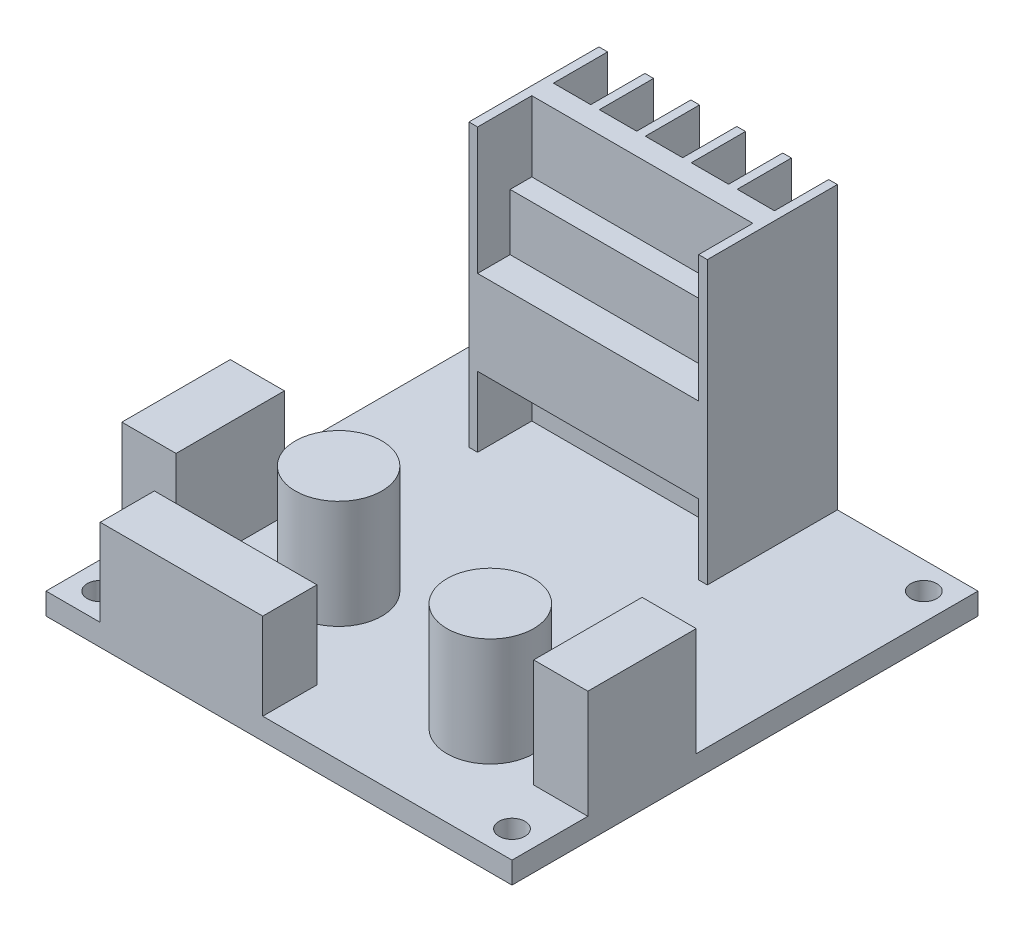
SolidWorks part; units mm, degrees
ref_plane "前视基准面" through (0, 0, 0) normal (0, 0, 1) x (1, 0, 0)
ref_plane "上视基准面" through (0, 0, 0) normal (0, 1, 0) x (1, 0, 0)
ref_plane "右视基准面" through (0, 0, 0) normal (1, 0, 0) x (0, 0, -1)
sketch "草图1" plane through (0, 0, 0) normal (0, 1, 0) x (1, 0, 0)
  line L1 (-21.5, 21.5) -> (21.5, 21.5)
  line L2 (-21.5, 21.5) -> (-21.5, -21.5)
  line L3 (-21.5, -21.5) -> (21.5, -21.5)
  line L4 (21.5, 21.5) -> (21.5, -21.5)
  dimension "D1" = 43
  dimension "D2" = 43
  dimension "D3" = 21.5
  dimension "D4" = 21.5
extrude "凸台-拉伸1" add sketch "草图1" along normal blind 2
sketch "草图2" plane through (0, 0, 0) normal (0, 1, 0) x (1, 0, 0)
  line L0 (-21.5, -21.5) -> (21.5, -21.5) construction
  line L1 (-16.5, -16.5) -> (-1.5, -16.5)
  line L2 (-16.5, -16.5) -> (-16.5, -21.5)
  line L3 (-16.5, -21.5) -> (-1.5, -21.5)
  line L4 (-1.5, -16.5) -> (-1.5, -21.5)
  line L5 (-21.5, 21.5) -> (-21.5, -21.5) construction
  dimension "D1" = 5
  dimension "D2" = 15
  dimension "D3" = 5
extrude "凸台-拉伸2" add sketch "草图2" along normal blind 10
sketch "草图3" plane through (0, 2, 0) normal (0, 1, 0) x (1, 0, 0)
  line L0 (-21.5, 21.5) -> (-21.5, -21.5) construction
  line L1 (-16.5, -4.5) -> (-21.5, -4.5)
  line L2 (-16.5, -4.5) -> (-16.5, -14.5)
  line L3 (-16.5, -14.5) -> (-21.5, -14.5)
  line L4 (-21.5, -4.5) -> (-21.5, -14.5)
  line L5 (-21.5, -21.5) -> (-16.5, -21.5) construction
  dimension "D1" = 7
  dimension "D2" = 5
  dimension "D3" = 10
extrude "凸台-拉伸3" add sketch "草图3" along normal blind 10
sketch "草图4" plane through (0, 2, 0) normal (0, 1, 0) x (1, 0, 0)
  line L0 (21.5, -21.5) -> (21.5, 21.5) construction
  line L1 (16.5, -4.5) -> (21.5, -4.5)
  line L2 (16.5, -4.5) -> (16.5, -14.5)
  line L3 (16.5, -14.5) -> (21.5, -14.5)
  line L4 (21.5, -4.5) -> (21.5, -14.5)
  line L5 (-1.5, -21.5) -> (21.5, -21.5) construction
  dimension "D1" = 7
  dimension "D2" = 10
  dimension "D3" = 5
extrude "凸台-拉伸4" add sketch "草图4" along normal blind 10
sketch "草图5" plane through (0, 2, 0) normal (0, 1, 0) x (1, 0, 0)
  circle A0 centre (-8, -8) radius 4
  point P2 (0, 0)
  point P3 (-6.2464, -8.5132)
  point P4 (0, 0)
  point P5 (0, 0)
extrude "凸台-拉伸5" add sketch "草图5" along normal blind 10
sketch "草图6" plane through (0, 2, 0) normal (0, 1, 0) x (1, 0, 0)
  circle A0 centre (10, -12) radius 4
extrude "凸台-拉伸6" add sketch "草图6" along normal blind 10
sketch "草图7" plane through (0, 2, 0) normal (0, 1, 0) x (1, 0, 0)
  line L0 (21.5, 21.5) -> (-21.5, 21.5) construction
  line L1 (0, 21.5) -> (-13.4757, 21.5)
  line L3 (8.5243, 9.5) -> (-13.4757, 9.5)
  line L4 (-13.4757, 21.5) -> (-13.4757, 9.5)
  line L5 (8.5243, 9.5) -> (8.5243, 21.5)
  line L6 (8.5243, 21.5) -> (-13.4757, 21.5)
extrude "凸台-拉伸7" add sketch "草图7" along normal blind 26 contours L4 L3 L5 L6
sketch "草图8" plane through (0, 0, -21.5) normal (0, 0, -1) x (-1, 0, 0)
  line L0 (-8.5243, 28) -> (13.4757, 28) construction
  line L1 (12.6757, 28) -> (9.2357, 28)
  line L2 (12.6757, 28) -> (12.6757, 2)
  line L3 (12.6757, 2) -> (9.2357, 2)
  line L4 (9.2357, 28) -> (9.2357, 2)
  line L5 (13.4757, 28) -> (13.4757, 2) construction
  line L7 (8.4357, 28) -> (4.9957, 28)
  line L8 (8.4357, 28) -> (8.4357, 1.9448)
  line L9 (8.4357, 1.9448) -> (4.9957, 1.9448)
  line L10 (4.9957, 28) -> (4.9957, 1.9448)
  line L11 (4.1957, 28) -> (0.7557, 28)
  line L12 (4.1957, 28) -> (4.1957, 2)
  line L13 (4.1957, 2) -> (0.7557, 2)
  line L14 (0.7557, 28) -> (0.7557, 2)
  line L15 (-0.0443, 28) -> (-3.4843, 28)
  line L16 (-0.0443, 28) -> (-0.0443, 2)
  line L17 (-0.0443, 2) -> (-3.4843, 2)
  line L18 (-3.4843, 28) -> (-3.4843, 2)
  line L19 (-4.2843, 28) -> (-7.7243, 28)
  line L20 (-4.2843, 28) -> (-4.2843, 2)
  line L21 (-4.2843, 2) -> (-7.7243, 2)
  line L22 (-7.7243, 28) -> (-7.7243, 2)
  dimension "D1" = 0.8
  dimension "D2" = 26
  dimension "D3" = 26
  dimension "D4" = 26
  dimension "D5" = 26
  dimension "D6" = 0.8
  dimension "D7" = 3.44
  dimension "3" = 3.44
  dimension "D8" = 3.44
  dimension "D9" = 0.8
  dimension "26" = 26.0552
  dimension "D10" = 0.8
  dimension "D11" = 3.44
  dimension "D12" = 0.8
  dimension "D13" = 3.44
sketch "草图9" plane through (0, 0, -21.5) normal (0, 0, -1) x (-1, 0, 0)
extrude "切除-拉伸1" cut sketch "草图8" against normal blind 5
sketch "草图11" plane through (0, 0, -9.5) normal (0, 0, 1) x (1, 0, 0)
  line L0 (8.5243, 28) -> (-13.4757, 28) construction
  line L1 (-12.6757, 28) -> (7.7243, 28)
  line L2 (-12.6757, 28) -> (-12.6757, 2)
  line L3 (-12.6757, 2) -> (7.7243, 2)
  line L4 (7.7243, 28) -> (7.7243, 2)
  line L5 (8.5243, 2) -> (-13.4757, 2) construction
  line L6 (-13.4757, 28) -> (-13.4757, 2) construction
  line L7 (8.5243, 28) -> (8.5243, 2) construction
  dimension "D1" = 0.8
  dimension "D2" = 0.8
extrude "切除-拉伸2" cut sketch "草图11" against normal blind 5
sketch "草图12" plane through (0, 0, -14.5) normal (0, 0, 1) x (1, 0, 0)
  line L0 (-12.6757, 28) -> (-12.6757, 2) construction
  line L1 (-12.6757, 16.2949) -> (7.7243, 16.2949)
  line L2 (-12.6757, 16.2949) -> (-12.6757, 8.4727)
  line L3 (-12.6757, 8.4727) -> (7.7243, 8.4727)
  line L4 (7.7243, 16.2949) -> (7.7243, 8.4727)
extrude "凸台-拉伸8" add sketch "草图12" along normal blind 5 contours L2 L1 L4 L3
sketch "草图13" plane through (0, 0, -14.5) normal (0, 0, 1) x (1, 0, 0)
  line L0 (7.7243, 16.2949) -> (7.7243, 28) construction
  line L1 (7.7243, 21.5097) -> (-12.6757, 21.5097)
  line L2 (7.7243, 21.5097) -> (7.7243, 16.2949)
  line L3 (7.7243, 16.2949) -> (-12.6757, 16.2949)
  line L4 (-12.6757, 21.5097) -> (-12.6757, 16.2949)
  line L5 (-12.6757, 16.2949) -> (7.7243, 16.2949) construction
extrude "凸台-拉伸9" add sketch "草图13" along normal blind 2
sketch "草图14" plane through (0, 2, 0) normal (0, 1, 0) x (1, 0, 0)
  line L0 (21.5, -4.5) -> (21.5, 21.5) construction
  line L1 (-19, 19) -> (19, 19) construction
  line L2 (-19, 19) -> (-19, -19) construction
  line L3 (-19, -19) -> (19, -19) construction
  line L4 (19, 19) -> (19, -19) construction
  line L5 (-13.4757, 21.5) -> (-21.5, 21.5) construction
  line L6 (-21.5, 21.5) -> (-21.5, -4.5) construction
  line L7 (-1.5, -21.5) -> (21.5, -21.5) construction
  circle A0 centre (-19, 19) radius 1.2
  circle A1 centre (19, 19) radius 1.2
  circle A2 centre (-19, -19) radius 1.2
  circle A3 centre (19, -19) radius 1.2
  dimension "D1" = 2.5
  dimension "D2" = 2.5
  dimension "D3" = 2.5
  dimension "D4" = 2.5
extrude "切除-拉伸3" cut sketch "草图14" against normal blind 2
